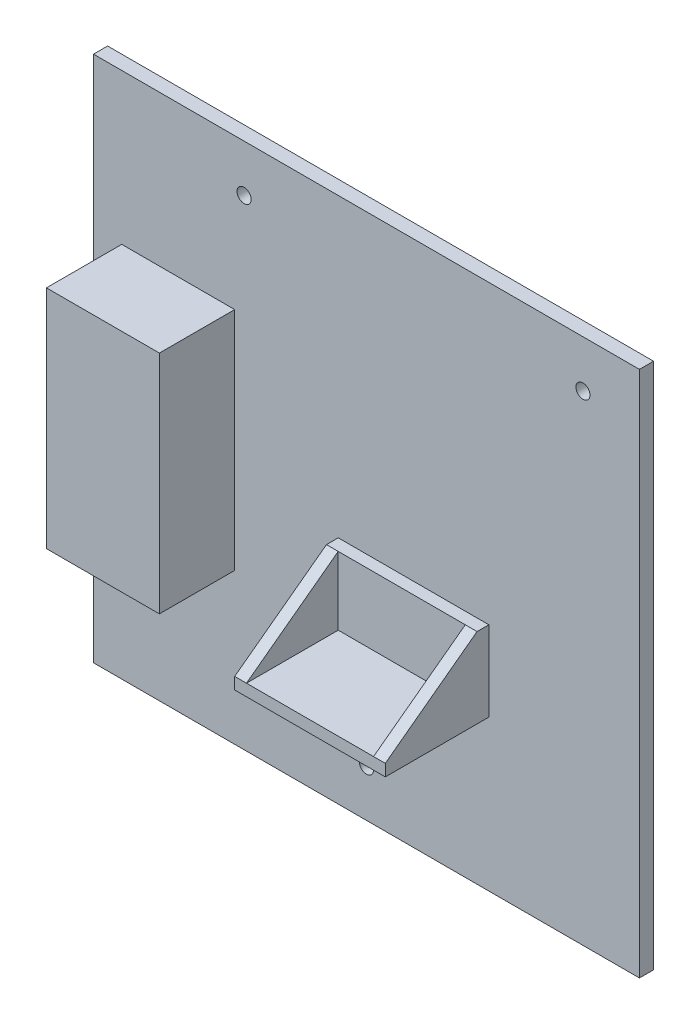
SolidWorks part; units mm, degrees
ref_plane "Front" through (0, 0, 0) normal (0, 0, 1) x (1, 0, 0)
ref_plane "Top" through (0, 0, 0) normal (0, 1, 0) x (1, 0, 0)
ref_plane "Right" through (0, 0, 0) normal (1, 0, 0) x (0, 0, -1)
sketch "Sketch1" plane through (0, 0, 0) normal (0, 0, 1) x (1, 0, 0)
  line L1 (-58, -56) -> (58, -56)
  line L2 (-58, -56) -> (-58, 56)
  line L3 (-58, 56) -> (58, 56)
  line L4 (58, -56) -> (58, 56)
  line L5 (-58, -56) -> (58, 56) construction
  line L6 (-58, 56) -> (58, -56) construction
  point P0 (0, 0)
  dimension "D1" = 112
  dimension "D2" = 116
extrude "Boss-Extrude1" add sketch "Sketch1" along normal blind 3
sketch "Sketch2" plane through (0, 0, 3) normal (0, 0, 1) x (1, 0, 0)
  line L0 (-58, 56) -> (-58, -56) construction
  line L1 (-52, -24) -> (-28, -24)
  line L2 (-52, -24) -> (-52, 24)
  line L3 (-52, 24) -> (-28, 24)
  line L4 (-28, -24) -> (-28, 24)
  line L5 (-52, -24) -> (-28, 24) construction
  line L6 (-52, 24) -> (-28, -24) construction
  point P0 (-40, 0)
  dimension "D1" = 48
  dimension "D2" = 24
  dimension "D3" = 6
extrude "Boss-Extrude2" add sketch "Sketch2" along normal blind 16
sketch "Sketch3" plane through (0, 0, 3) normal (0, 0, 1) x (1, 0, 0)
  line L0 (-52, -24) -> (-28, -24) construction
  line L1 (-6, -24) -> (26, -24)
  line L2 (-6, -24) -> (-6, -7)
  line L3 (-6, -7) -> (26, -7)
  line L4 (26, -24) -> (26, -7)
  line L5 (-6, -24) -> (26, -7) construction
  line L6 (-6, -7) -> (26, -24) construction
  point P0 (10, -15.5)
  dimension "D1" = 17
  dimension "D2" = 32
  dimension "D3" = 10
extrude "Boss-Extrude3" add sketch "Sketch3" along normal blind 22
sketch "Sketch4" plane through (26, 0, 0) normal (1, 0, 0) x (0, 0, -1)
  line L0 (-25, -24) -> (-25, -21.5) construction
  line L1 (-25, -24) -> (-25, -7) construction
  line L2 (-25, -21.5) -> (-5.5, -7)
  line L3 (-25, -7) -> (-3, -7) construction
  line L4 (-3, -24) -> (-3, 24) construction
  line L5 (-25, -21.5) -> (-25, -7)
  line L6 (-25, -7) -> (-5.5, -7)
  dimension "D1" = 2.5
  dimension "D2" = 2.5
extrude "Cut-Extrude1" cut sketch "Sketch4" against normal up to next
sketch "Sketch5" plane through (0, 0, 25) normal (0, 0, 1) x (1, 0, 0)
  line L2 (-3.5, -7) -> (-3.5, -24)
  line L3 (-3.5, -7) -> (-3.5, -21.5)
  line L4 (23.5, -21.5) -> (-3.5, -21.5)
  line L5 (23.5, -21.5) -> (23.5, -7)
  line L6 (23.5, -21.5) -> (23.5, -7)
  line L7 (-6, -21.5) -> (26, -21.5) construction
  line L8 (-3.5, -7) -> (23.5, -7)
  dimension "D1" = 2.5
  dimension "D2" = 2.5
extrude "Cut-Extrude2" cut sketch "Sketch5" against normal blind 19.5
sketch "Sketch6" plane through (0, 0, 3) normal (0, 0, 1) x (1, 0, 0)
  line L0 (-58, 56) -> (-58, -56) construction
  line L1 (58, -56) -> (58, 56) construction
  line L2 (58, 56) -> (-58, 56) construction
  line L3 (-58, -56) -> (58, -56) construction
  circle A0 centre (-26, 46) radius 1.5
  circle A1 centre (46, 46) radius 1.5
  circle A2 centre (0, -46) radius 1.5
  dimension "D1" = 3
  dimension "D2" = 3
  dimension "D3" = 3
  dimension "D5" = 12
  dimension "D4" = 32
  dimension "D6" = 10
  dimension "D7" = 10
extrude "Cut-Extrude3" cut sketch "Sketch6" against normal up to next
